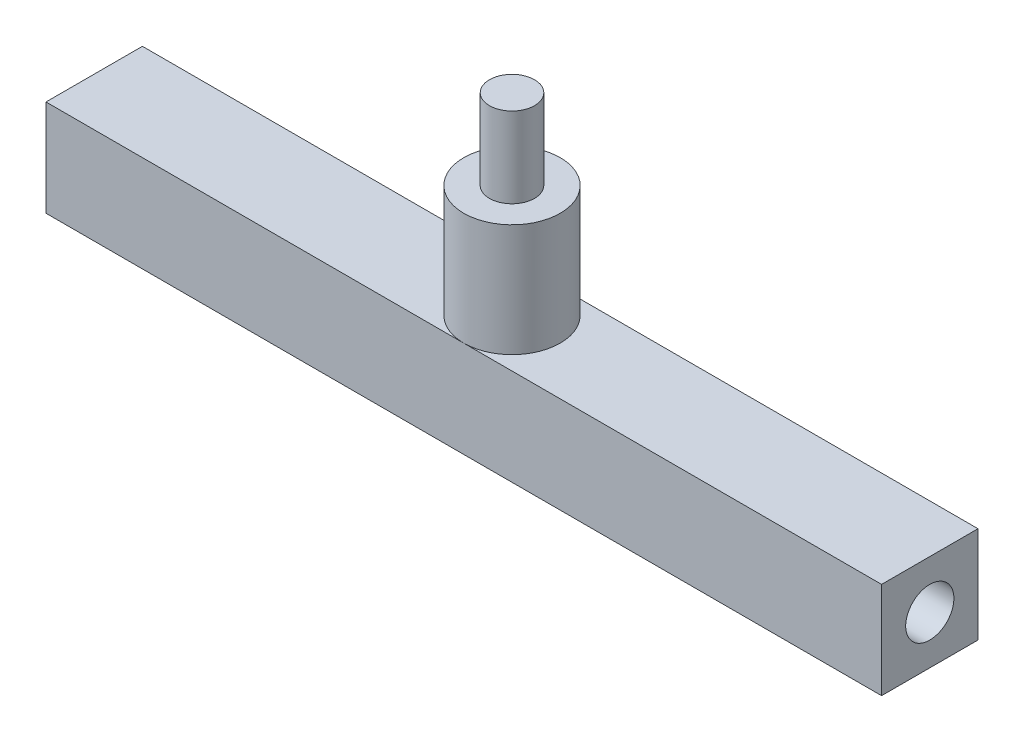
SolidWorks part; units mm, degrees
ref_plane "Front Plane" through (0, 0, 0) normal (0, 0, 1) x (1, 0, 0)
ref_plane "Top Plane" through (0, 0, 0) normal (0, 1, 0) x (1, 0, 0)
ref_plane "Right Plane" through (0, 0, 0) normal (1, 0, 0) x (0, 0, -1)
sketch "Sketch1" plane through (0, 0, 0) normal (0, 1, 0) x (1, 0, 0)
  line L1 (0, 0) -> (52, 0)
  line L2 (0, 0) -> (0, 6)
  line L3 (0, 6) -> (52, 6)
  line L4 (52, 0) -> (52, 6)
  dimension "D1" = 6
  dimension "D2" = 52
extrude "Boss-Extrude1" add sketch "Sketch1" along normal blind 6
sketch "Sketch2" plane through (0, 6, 0) normal (0, 1, 0) x (1, 0, 0)
  line L0 (0, 3) -> (52, 3) construction
  line L1 (0, 6) -> (0, 0) construction
  line L2 (52, 0) -> (52, 6) construction
  circle A0 centre (26, 3) radius 3
  dimension "D1" = 6
extrude "Boss-Extrude2" add sketch "Sketch2" along normal blind 7
sketch "Sketch3" plane through (0, 13, 0) normal (0, 1, 0) x (1, 0, 0)
  circle A0 centre (26, 3) radius 1.4
  dimension "D1" = 2.8
extrude "Boss-Extrude3" add sketch "Sketch3" along normal blind 5
hole_wizard "M3x0.5 Tapped Hole1" positions "Sketch4" profile "Sketch5" tap size "M3x0.5" standard "ANSI Metric"
sketch "Sketch4" plane through (52, 0, 0) normal (1, 0, 0) x (0, 0, -1)
  line L0 (3, 6) -> (3, 0) construction
  line L1 (0, 6) -> (6, 6) construction
  line L2 (0, 0) -> (6, 0) construction
  line L5 (6, 3) -> (0, 3) construction
  line L6 (6, 6) -> (6, 0) construction
  line L7 (0, 6) -> (0, 0) construction
  point P20 (3, 3)
sketch "Sketch5" plane through (52, 3, -3) normal (0, 1, 0) x (0, 0, -1)
  line L0 (0, 0) -> (0, 8.2511)
  line L1 (0, 8.2511) -> (1.25, 7.5)
  line L2 (1.25, 7.5) -> (1.25, 6)
  line L3 (1.25, 6) -> (1.5, 6)
  line L4 (1.5, 6) -> (1.5, 0)
  line L5 (1.5, 0) -> (0, 0)
  line L10 (0, 8.2511) -> (-1.25, 7.5) construction
  line L11 (0, -6.35) -> (0, 107.95) construction
  dimension "Tap Drill Dia." = 2.5
  dimension "Tap Drill Depth" = 7.5
  dimension "Thread Major Dia." = 3
  dimension "Thread Depth" = 6
  dimension "Drill Angle" = 118
hole_wizard "M3x0.5 Tapped Hole2" positions "Sketch6" profile "Sketch7" tap size "M3x0.5" standard "ANSI Metric"
sketch "Sketch6" plane through (0, 0, 0) normal (-1, 0, 0) x (0, 0, 1)
  point P0 (-3, 3)
sketch "Sketch7" plane through (0, 3, -3) normal (0, 1, 0) x (0, 0, 1)
  line L0 (0, 0) -> (0, 8.2511)
  line L1 (0, 8.2511) -> (1.25, 7.5)
  line L2 (1.25, 7.5) -> (1.25, 6)
  line L3 (1.25, 6) -> (1.5, 6)
  line L4 (1.5, 6) -> (1.5, 0)
  line L5 (1.5, 0) -> (0, 0)
  line L10 (0, 8.2511) -> (-1.25, 7.5) construction
  line L11 (0, -6.35) -> (0, 107.95) construction
  dimension "Tap Drill Dia." = 2.5
  dimension "Tap Drill Depth" = 7.5
  dimension "Thread Major Dia." = 3
  dimension "Thread Depth" = 6
  dimension "Drill Angle" = 118
